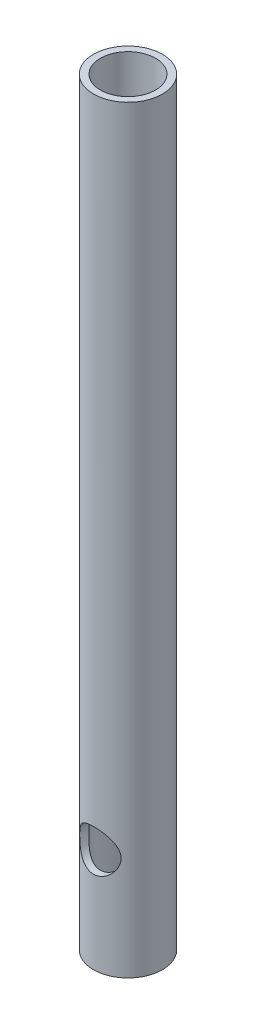
SolidWorks part; units mm, degrees
ref_plane "Front Plane" through (0, 0, 0) normal (0, 0, 1) x (1, 0, 0)
ref_plane "Top Plane" through (0, 0, 0) normal (0, 1, 0) x (1, 0, 0)
ref_plane "Right Plane" through (0, 0, 0) normal (1, 0, 0) x (0, 0, -1)
sketch "Sketch1" plane through (0, 126.4508, 0) normal (0, 1, 0) x (1, 0, 0)
  circle A0 centre (87.7299, -127.8079) radius 5
  circle A1 centre (87.7299, -127.8079) radius 4
  dimension "D1" = 8
  dimension "D2" = 10
extrude "Boss-Extrude1" add sketch "Sketch1" along normal blind 80 and the other way blind 30
sketch "Sketch2" plane through (-5.567, 0.1107, 127.8079) normal (0, 0, -1) x (-1, 0, 0)
  circle A0 centre (-93.2969, 111.3401) radius 3
  dimension "D1" = 6
extrude "Cut-Extrude1" cut sketch "Sketch2" against normal through all both and the other way through all
